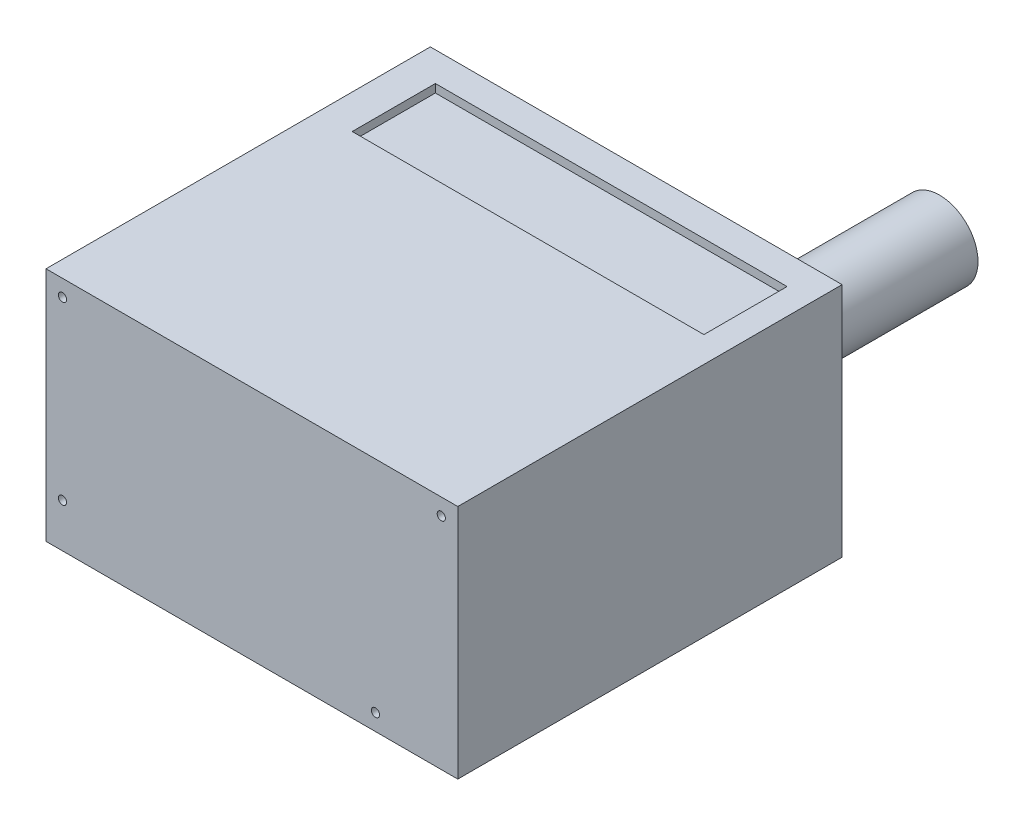
SolidWorks part; units mm, degrees
ref_plane "Front Plane" through (0, 0, 0) normal (0, 0, 1) x (1, 0, 0)
ref_plane "Top Plane" through (0, 0, 0) normal (0, 1, 0) x (1, 0, 0)
ref_plane "Right Plane" through (0, 0, 0) normal (1, 0, 0) x (0, 0, -1)
sketch "Sketch1" plane through (0, 0, 0) normal (0, 1, 0) x (1, 0, 0)
  line L1 (0, 0) -> (150, 0)
  line L2 (0, 0) -> (0, 140)
  line L3 (0, 140) -> (150, 140)
  line L4 (150, 0) -> (150, 140)
  dimension "D1" = 150
  dimension "D2" = 140
extrude "Boss-Extrude1" add sketch "Sketch1" along normal blind 86
sketch "Sketch2" plane through (0, 0, 0) normal (0, 0, 1) x (1, 0, 0)
  line L0 (0, 86) -> (150, 86) construction
  line L1 (0, 86) -> (0, 0) construction
  line L2 (0, 0) -> (150, 0) construction
  line L3 (150, 86) -> (150, 0) construction
  circle A0 centre (6, 80) radius 1.5
  circle A1 centre (6, 16) radius 1.5
  circle A2 centre (120, 6) radius 1.5
  circle A3 centre (144, 80) radius 1.5
  dimension "D1" = 6
  dimension "D2" = 64
  dimension "D5" = 114
  dimension "D7" = 6
  dimension "D3" = 6
  dimension "D4" = 6
  dimension "D6" = 6
  dimension "D8" = 6
extrude "Cut-Extrude1" cut sketch "Sketch2" against normal blind 3
ref_plane "Plane1" through (0, 86, 0) normal (0, 1, 0) x (1, 0, 0)
sketch "bottom vent" plane through (0, 86, 0) normal (0, 1, 0) x (1, 0, 0)
  line L1 (12.4737, 129.368) -> (140.586, 129.368)
  line L2 (12.4737, 129.368) -> (12.4737, 99.0671)
  line L3 (12.4737, 99.0671) -> (140.586, 99.0671)
  line L4 (140.586, 129.368) -> (140.586, 99.0671)
extrude "Cut-Extrude2" cut sketch "bottom vent" against normal blind 3
ref_plane "Plane2" through (0, 0, -140) normal (0, 0, -1) x (-1, 0, 0)
sketch "Sketch4" plane through (0, 0, -140) normal (0, 0, -1) x (-1, 0, 0)
  line L0 (-150, 86) -> (-150, 0) construction
  line L1 (77, 86) -> (-77, 86) construction
  circle A0 centre (-133.5, 66) radius 14
  dimension "D1" = 16.5
  dimension "D2" = 20
extrude "Boss-Extrude2" add sketch "Sketch4" along normal blind 52
sketch "Sketch5" plane through (0, 0, -140) normal (0, 0, -1) x (-1, 0, 0)
  line L1 (-15.7497, 77.9101) -> (-114.6095, 77.9101)
  line L2 (-15.7497, 77.9101) -> (-15.7497, 5.9003)
  line L3 (-15.7497, 5.9003) -> (-114.6095, 5.9003)
  line L4 (-114.6095, 77.9101) -> (-114.6095, 5.9003)
extrude "Cut-Extrude3" cut sketch "Sketch5" against normal blind 3
